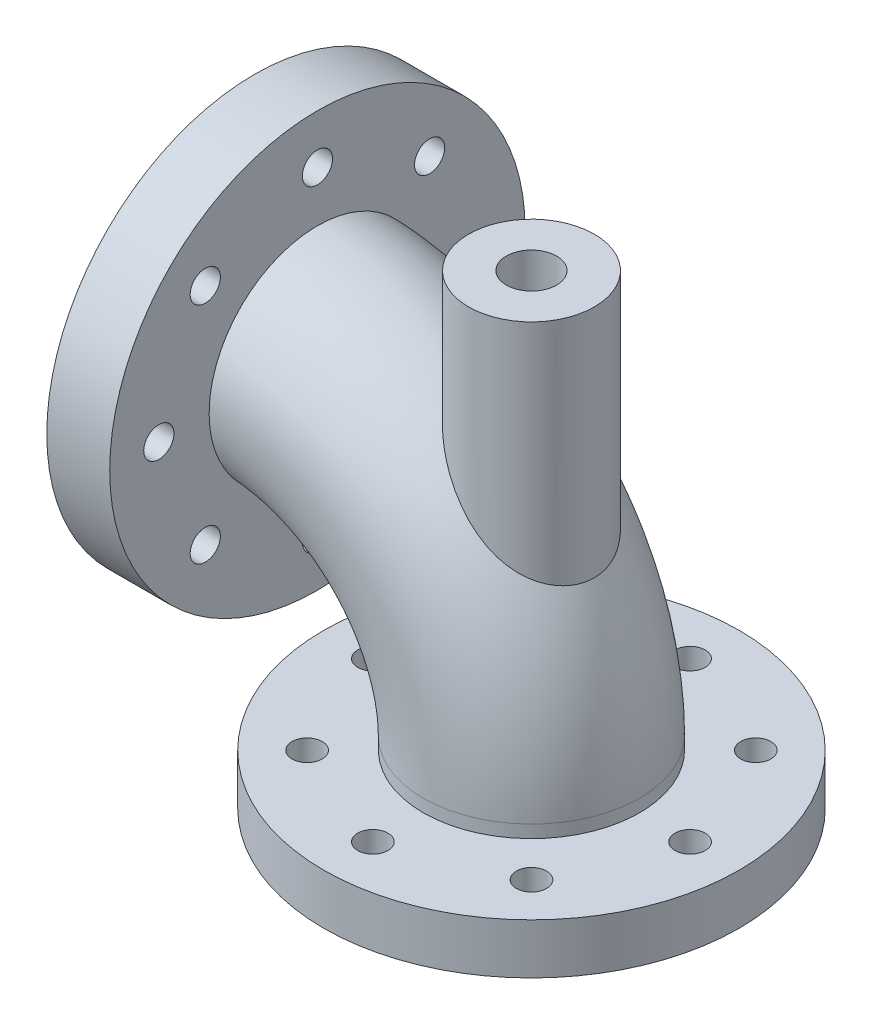
SolidWorks part; units mm, degrees
ref_plane "Front Plane" through (0, 0, 0) normal (0, 0, 1) x (1, 0, 0)
ref_plane "Top Plane" through (0, 0, 0) normal (0, 1, 0) x (1, 0, 0)
ref_plane "Right Plane" through (0, 0, 0) normal (1, 0, 0) x (0, 0, -1)
sketch "Sketch5" plane through (0, 0, 0) normal (0, 0, 1) x (1, 0, 0)
  line L0 (0, 0) -> (0, 25)
  line L1 (-90, 115) -> (-110, 115)
  arc A0 (0, 25) -> (-90, 115) centre (-90, 25) ccw
  dimension "D3" = 90
  dimension "D1" = 20
  dimension "D2" = 25
sketch "Sketch6" plane through (0, 0, 0) normal (0, 1, 0) x (1, 0, 0)
  circle A0 centre (0, 0) radius 43
  dimension "D1" = 86
sweep "Sweep-Thin1" add profiles "Sketch6" path "Sketch5" parameters "D1"=16
ref_plane "Plane1" through (0, 185, 0) normal (0, -1, 0) x (-1, 0, 0)
sketch "Sketch7" plane through (0, 185, 0) normal (0, -1, 0) x (-1, 0, 0)
  circle A0 centre (0, 0) radius 25
  dimension "D1" = 50
extrude "Boss-Extrude1" add sketch "Sketch7" along normal up to next
sketch "Sketch8" plane through (0, 185, 0) normal (0, 1, 0) x (1, 0, 0)
  circle A0 centre (0, 0) radius 10
  dimension "D1" = 20
extrude "Cut-Extrude1" cut sketch "Sketch8" against normal up to next
sketch "Sketch9" plane through (0, 0, 0) normal (0, -1, 0) x (1, 0, 0)
  circle A0 centre (0, 0) radius 82.5
  dimension "D1" = 165
extrude "Boss-Extrude2" add sketch "Sketch9" against normal blind 20
sketch "Sketch10" plane through (0, 0, 0) normal (0, -1, 0) x (1, 0, 0)
  circle A0 centre (0, 0) radius 27
  dimension "D1" = 54
extrude "Cut-Extrude2" cut sketch "Sketch10" against normal blind 20
sketch "Sketch11" plane through (0, 0, 0) normal (0, -1, 0) x (1, 0, 0)
  circle A0 centre (0, 0) radius 63 construction
  circle A1 centre (-63, 0) radius 6
  circle A2 centre (-44.5477, 44.5477) radius 6
  circle A3 centre (0, 63) radius 6
  circle A4 centre (44.5477, 44.5477) radius 6
  circle A5 centre (63, 0) radius 6
  circle A6 centre (44.5477, -44.5477) radius 6
  circle A7 centre (0, -63) radius 6
  circle A8 centre (-44.5477, -44.5477) radius 6
  point P21 (0, 0)
  dimension "D1" = 126
  dimension "D2" = 12
  dimension "D3" = 8
extrude "Cut-Extrude3" cut sketch "Sketch11" against normal blind 20
sketch "Sketch12" plane through (-110, 0, 0) normal (-1, 0, 0) x (0, 0, 1)
  circle A0 centre (0, 115) radius 82.5
  dimension "D1" = 165
extrude "Boss-Extrude3" add sketch "Sketch12" against normal blind 25
sketch "Sketch13" plane through (-110, 0, 0) normal (-1, 0, 0) x (0, 0, 1)
  circle A0 centre (0, 115) radius 63 construction
  circle A1 centre (-63, 115) radius 6
  circle A2 centre (-44.5477, 159.5477) radius 6
  circle A3 centre (0, 178) radius 6
  circle A4 centre (44.5477, 159.5477) radius 6
  circle A5 centre (63, 115) radius 6
  circle A6 centre (44.5477, 70.4523) radius 6
  circle A7 centre (0, 52) radius 6
  circle A8 centre (-44.5477, 70.4523) radius 6
  point P21 (0, 115)
  dimension "D1" = 126
  dimension "D2" = 12
  dimension "D3" = 8
extrude "Cut-Extrude4" cut sketch "Sketch13" against normal blind 25
sketch "Sketch14" plane through (-110, 0, 0) normal (-1, 0, 0) x (0, 0, 1)
  circle A0 centre (0, 115) radius 27
  dimension "D1" = 54
extrude "Cut-Extrude5" cut sketch "Sketch14" against normal blind 25
